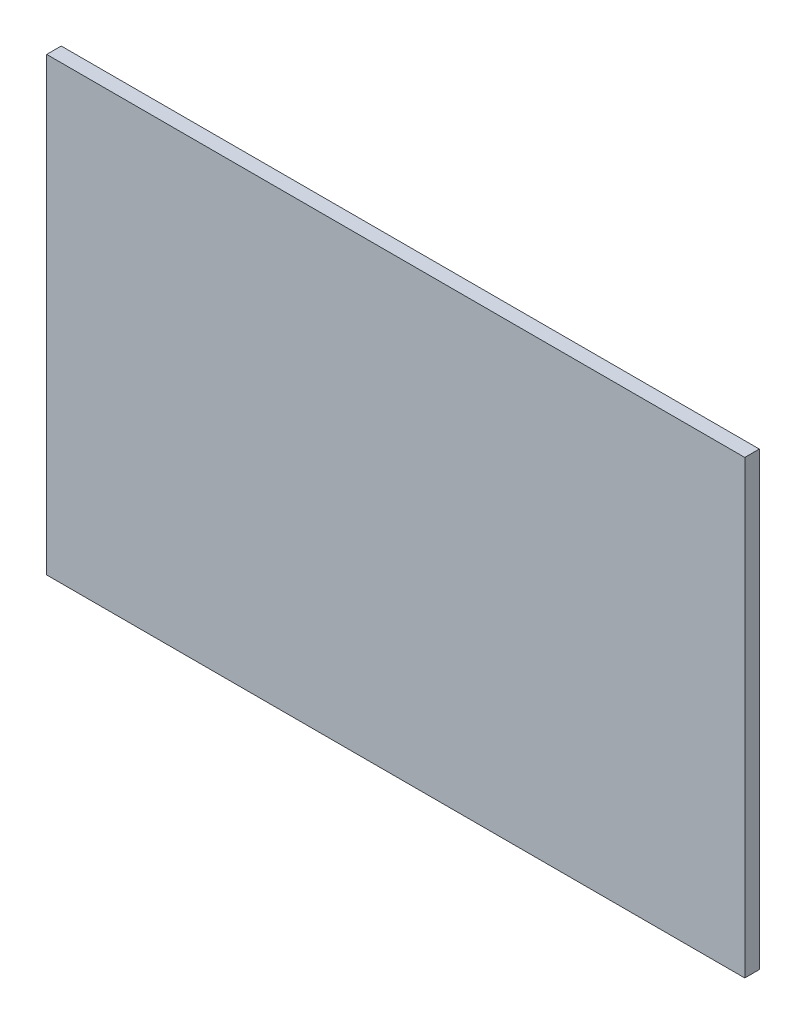
SolidWorks part; units mm, degrees
ref_plane "正面" through (0, 0, 0) normal (0, 0, 1) x (1, 0, 0)
ref_plane "平面" through (0, 0, 0) normal (0, 1, 0) x (1, 0, 0)
ref_plane "右側面" through (0, 0, 0) normal (1, 0, 0) x (0, 0, -1)
sketch "ｽｹｯﾁ1" plane through (0, 0, 0) normal (0, 0, 1) x (1, 0, 0)
  line L1 (-42.6888, 28.2642) -> (53.3112, 28.2642)
  line L2 (-42.6888, 28.2642) -> (-42.6888, -33.7358)
  line L3 (-42.6888, -33.7358) -> (53.3112, -33.7358)
  line L4 (53.3112, 28.2642) -> (53.3112, -33.7358)
  dimension "D1" = 96
  dimension "D2" = 62
extrude "ﾎﾞｽ - 押し出し1" add sketch "ｽｹｯﾁ1" along normal blind 2
